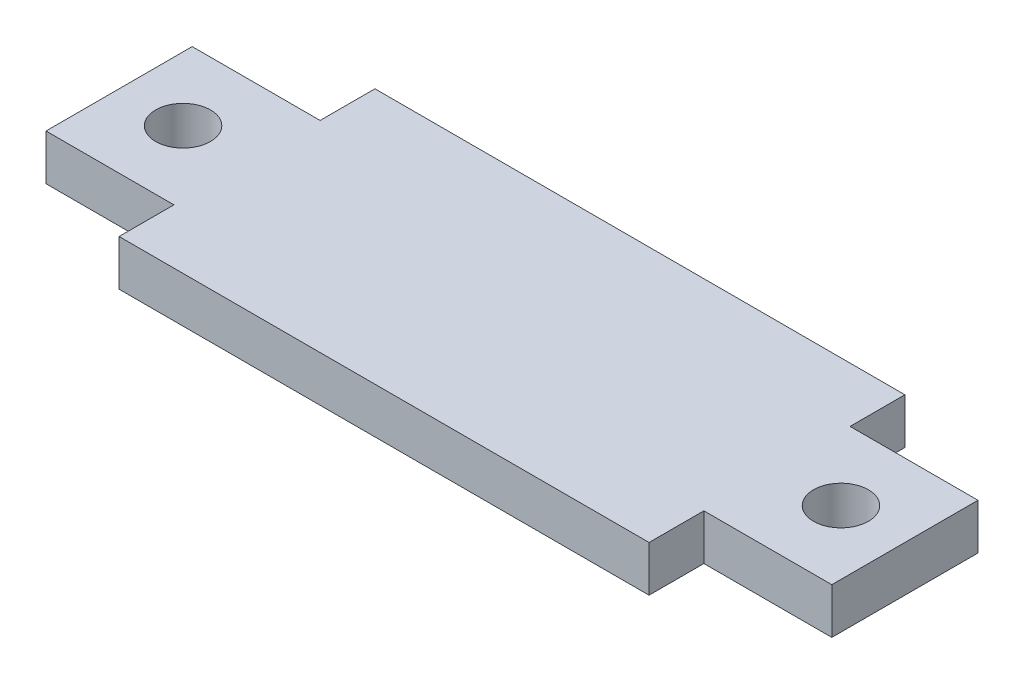
SolidWorks part; units mm, degrees
ref_plane "Front Plane" through (0, 0, 0) normal (0, 0, 1) x (1, 0, 0)
ref_plane "Top Plane" through (0, 0, 0) normal (0, 1, 0) x (1, 0, 0)
ref_plane "Right Plane" through (0, 0, 0) normal (1, 0, 0) x (0, 0, -1)
sketch "Sketch1" plane through (0, 0, 0) normal (0, 1, 0) x (1, 0, 0)
  line L1 (-14.5, 7) -> (14.5, 7)
  line L2 (-14.5, 7) -> (-14.5, -7)
  line L3 (-14.5, -7) -> (14.5, -7)
  line L4 (14.5, 7) -> (14.5, -7)
  line L5 (-14.5, 4) -> (-21.5, 4)
  line L6 (-14.5, 4) -> (-14.5, -4)
  line L7 (-14.5, -4) -> (-21.5, -4)
  line L8 (-21.5, 4) -> (-21.5, -4)
  line L9 (14.5, 4) -> (21.5, 4)
  line L10 (14.5, 4) -> (14.5, -4)
  line L11 (14.5, -4) -> (21.5, -4)
  line L12 (21.5, 4) -> (21.5, -4)
  circle A0 centre (-18, 0) radius 1.5
  circle A1 centre (18, 0) radius 1.5
  dimension "D11" = 3.5
  dimension "D12" = 7
  dimension "D13" = 3
  dimension "D14" = 7
  dimension "D15" = 3.5
  dimension "D16" = 3
  dimension "D1" = 14
  dimension "D2" = 29
  dimension "D3" = 14.5
  dimension "D4" = 7
  dimension "D5" = 3
  dimension "D6" = 3
  dimension "D7" = 7
  dimension "D8" = 3
  dimension "D9" = 3
  dimension "D10" = 7
extrude "Boss-Extrude1" add sketch "Sketch1" along normal blind 2.5 contours L4 L1 L2 L3 | L5 L8 L7 L2 A0 | L12 L9 L4 L11 A1
